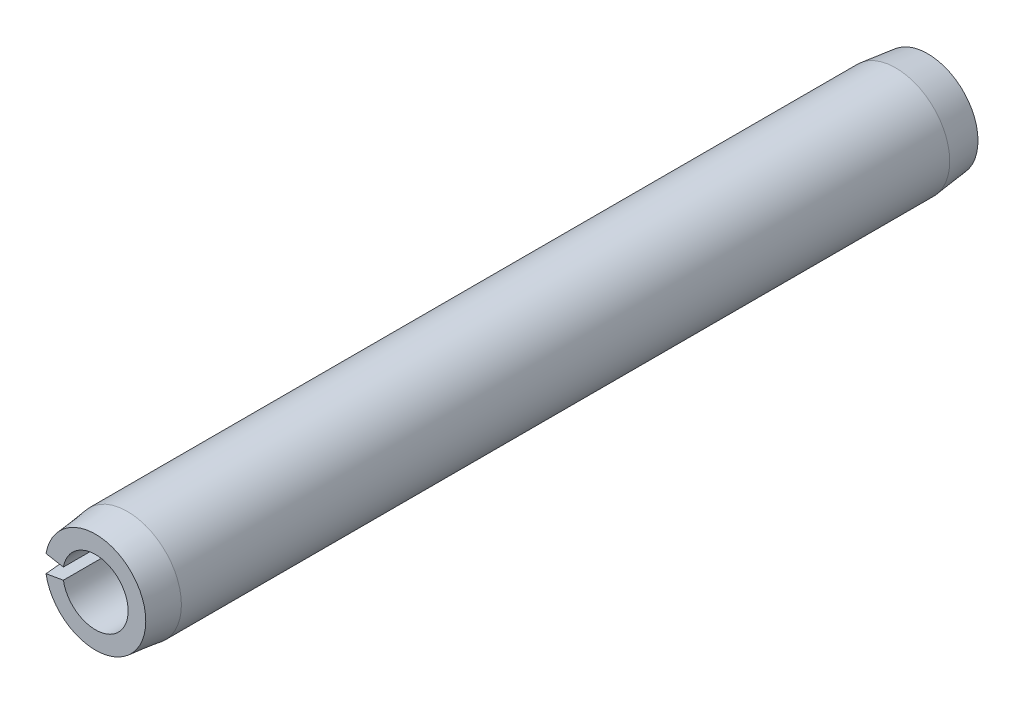
SolidWorks part; units mm, degrees
ref_plane "Front Plane" through (0, 0, 0) normal (0, 0, 1) x (1, 0, 0)
ref_plane "Top Plane" through (0, 0, 0) normal (0, 1, 0) x (1, 0, 0)
ref_plane "Right Plane" through (0, 0, 0) normal (1, 0, 0) x (0, 0, -1)
sketch "Sketch1" plane through (0, 0, 0) normal (0, 0, 1) x (1, 0, 0)
  line L0 (1.2446, 0) -> (2.0574, 0) construction
  line L1 (-2.0261, 0.3573) -> (-1.2257, 0.2161)
  line L2 (-1.2257, -0.2161) -> (-2.0261, -0.3573)
  arc A0 (-2.0261, -0.3573) -> (-2.0261, 0.3573) centre (0, 0) ccw
  arc A1 (-1.2257, -0.2161) -> (-1.2257, 0.2161) centre (0, 0) ccw
  dimension "OD" = 4.1148
  dimension "Wall thickness" = 0.8128
  dimension "D3" = 20
extrude "Extrude1" add sketch "Sketch1" along normal mid plane 31.75
sketch "Sketch2" plane through (0, 0, 0) normal (1, 0, 0) x (0, 0, -1)
  line L0 (0, -2.0574) -> (0, 2.0574) construction
  line L1 (15.875, 0) -> (-15.875, 0) construction
  line L2 (15.875, -1.2446) -> (15.875, 1.2446) construction
  line L3 (15.875, 2.0574) -> (-15.875, 2.0574) construction
  line L4 (15.875, 2.0574) -> (15.875, 1.9177)
  line L5 (15.875, 1.9177) -> (14.6558, 2.0574)
  line L6 (14.6558, 2.0574) -> (15.875, 2.0574)
  line L7 (15.875, -2.0574) -> (15.875, 2.0574) construction
  line L8 (-14.6558, 2.0574) -> (-15.875, 2.0574)
  line L9 (-15.875, 1.9177) -> (-14.6558, 2.0574)
  line L10 (-15.875, 2.0574) -> (-15.875, 1.9177)
  line L11 (14.6558, -2.0574) -> (15.875, -2.0574) construction
  line L12 (15.875, -1.9177) -> (14.6558, -2.0574) construction
  line L13 (15.875, -2.0574) -> (15.875, -1.9177) construction
  dimension "B" = 3.8354
  dimension "Chamfer max" = 1.2192
revolve "Cut-Revolve1" cut sketch "Sketch2" angle 360 about L1
sketch "Sketch3" plane through (0, 0, 0) normal (0, 0, 1) x (1, 0, 0)
  line L0 (1.2446, 0) -> (2.0574, 0) construction
  line L1 (1.2446, 0) -> (2.0574, 0)
  circle A0 centre (0, 0) radius 2.0574
  circle A1 centre (0, 0) radius 1.2446
  arc A2 (-2.0261, -0.3573) -> (-2.0261, 0.3573) centre (0, 0) ccw construction
  arc A3 (-1.2257, -0.2161) -> (-1.2257, 0.2161) centre (0, 0) ccw construction
